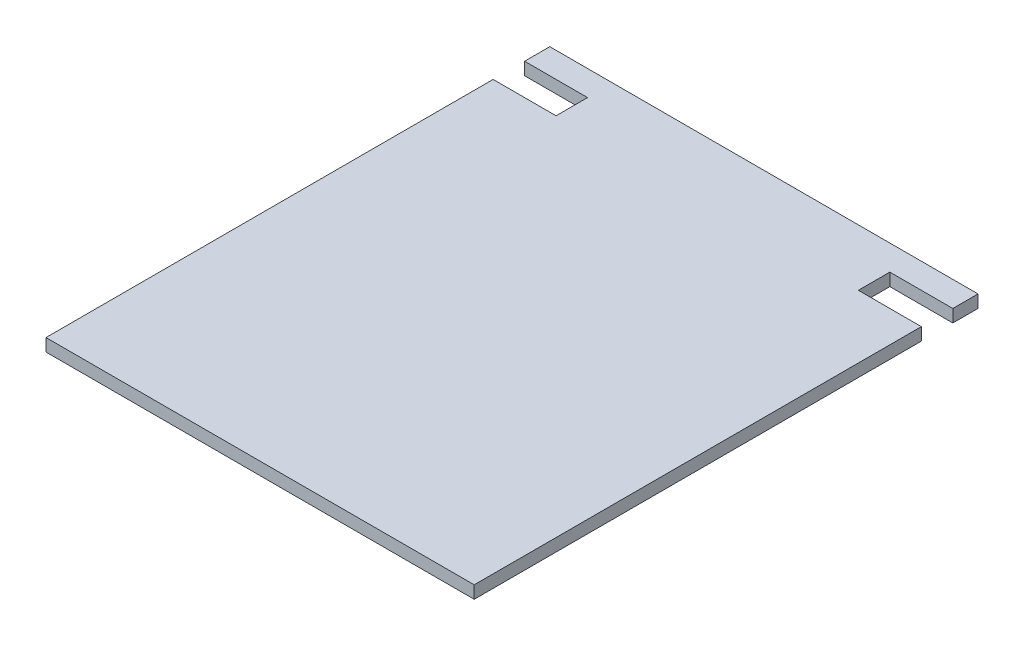
SolidWorks part; units mm, degrees
material "1060 Alloy"
ref_plane "Front Plane" through (0, 0, 0) normal (0, 0, 1) x (1, 0, 0)
ref_plane "Top Plane" through (0, 0, 0) normal (0, 1, 0) x (1, 0, 0)
ref_plane "Right Plane" through (0, 0, 0) normal (1, 0, 0) x (0, 0, -1)
sketch "Sketch2" plane through (0, 0, 0) normal (0, 1, 0) x (1, 0, 0)
  line L1 (-170, -200) -> (170, -200)
  line L2 (-170, -200) -> (-170, 200)
  line L3 (-170, 200) -> (170, 200)
  line L4 (170, -200) -> (170, 200)
  line L5 (-170, -200) -> (170, 200) construction
  line L6 (-170, 200) -> (170, -200) construction
  point P0 (0, 0)
extrude "Boss-Extrude1" add sketch "Sketch2" along normal blind 10
sketch "Sketch3" plane through (0, 10, 0) normal (0, 1, 0) x (1, 0, 0)
  line L6 (-170, 200) -> (-170, -200) construction
  line L7 (-170, 180) -> (-120, 180)
  line L8 (-120, 180) -> (-120, 155)
  line L9 (-120, 155) -> (-170, 155)
  line L10 (-170, 155) -> (-170, 180)
  line L11 (170, -200) -> (170, 200) construction
  line L12 (170, 180) -> (120, 180)
  line L13 (120, 180) -> (120, 155)
  line L14 (120, 155) -> (170, 155)
  line L15 (170, 155) -> (170, 180)
  point P0 (0, 0)
  dimension "D1" = 20
  dimension "D2" = 20
extrude "Cut-Extrude1" cut sketch "Sketch3" against normal blind 10
